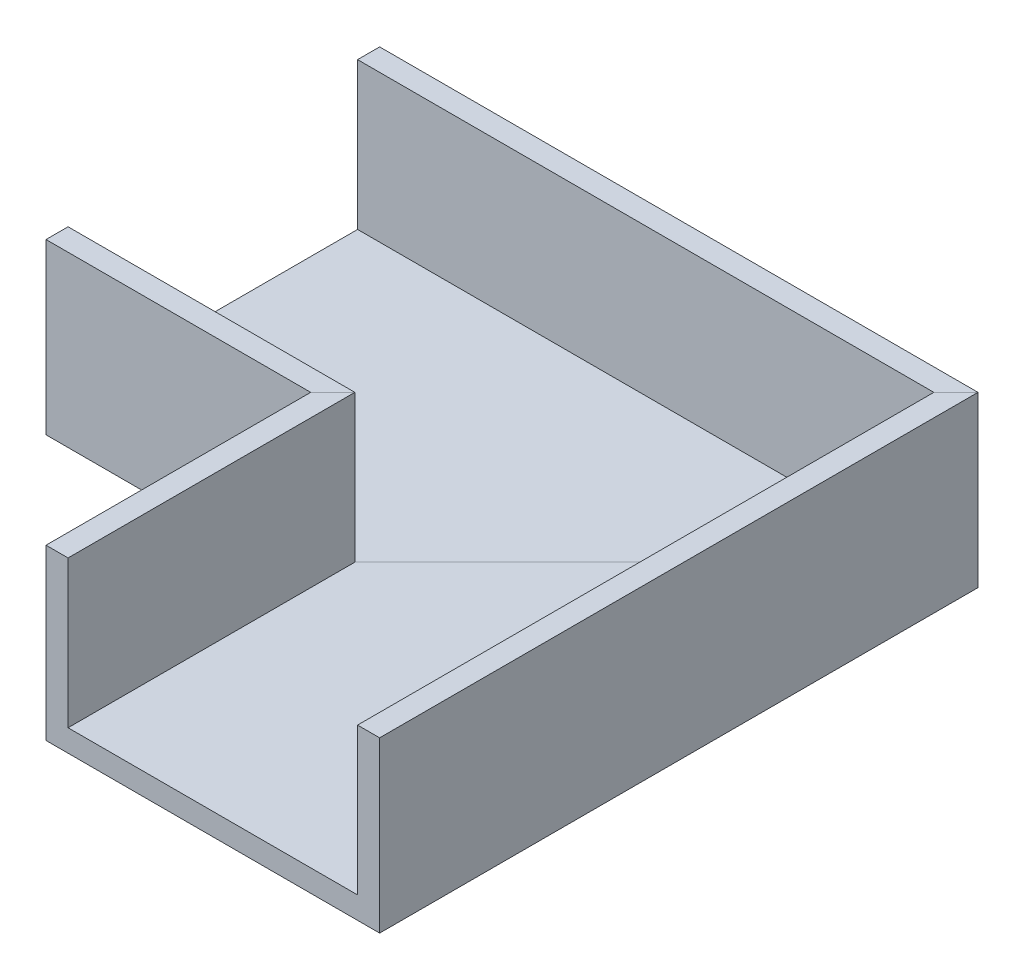
SolidWorks part; units mm, degrees
ref_plane "Front Plane" through (0, 0, 0) normal (0, 0, 1) x (1, 0, 0)
ref_plane "Top Plane" through (0, 0, 0) normal (0, 1, 0) x (1, 0, 0)
ref_plane "Right Plane" through (0, 0, 0) normal (1, 0, 0) x (0, 0, -1)
sketch "Sketch1" plane through (0, 0, 0) normal (0, 1, 0) x (1, 0, 0)
  line L0 (0, 0) -> (0, 36)
  line L1 (0, 36) -> (-36, 36)
  dimension "D1" = 36
  dimension "D2" = 36
sketch "Sketch2" plane through (0, 0, 0) normal (0, 0, 1) x (1, 0, 0)
  line L0 (0, 0) -> (0, 23)
  line L1 (0, 23) -> (3, 23)
  line L2 (3, 23) -> (3, 3)
  line L3 (3, 3) -> (42.37, 3)
  line L4 (42.37, 3) -> (42.37, 23)
  line L5 (42.37, 23) -> (45.37, 23)
  line L6 (45.37, 23) -> (45.37, 0)
  line L7 (45.37, 0) -> (0, 0)
  dimension "D1" = 39.37
  dimension "D2" = 3
  dimension "D3" = 3
  dimension "D4" = 3
  dimension "D5" = 20
sweep "Sweep1" add profiles "Sketch2" path "Sketch1"
